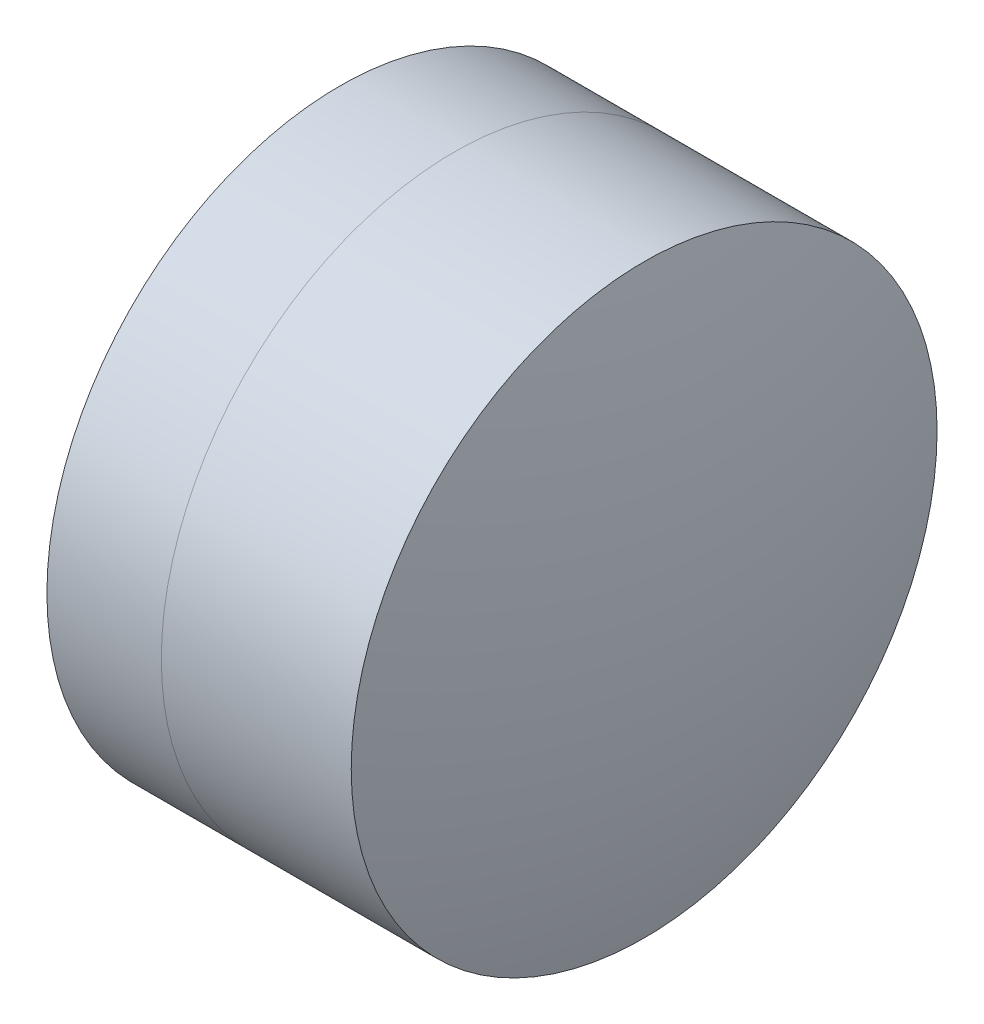
SolidWorks part; units mm, degrees
ref_plane "前视基准面" through (0, 0, 0) normal (0, 0, 1) x (1, 0, 0)
ref_plane "上视基准面" through (0, 0, 0) normal (0, 1, 0) x (1, 0, 0)
ref_plane "右视基准面" through (0, 0, 0) normal (1, 0, 0) x (0, 0, -1)
sketch "草图1" plane through (0, 0, 0) normal (0, 1, 0) x (1, 0, 0)
  line L0 (-0.8161, 0) -> (5.81, 0) construction
  line L1 (1.137, -3.175) -> (2.377, -3.175)
  line L2 (1.137, 3.175) -> (2.377, 3.175)
  arc A0 (2.377, -3.175) -> (2.377, 3.175) centre (-1.342, 0) ccw
  arc A1 (1.137, 3.175) -> (1.137, -3.175) centre (13.898, 0) ccw
  point P4 (5.81, 0)
  point P10 (0.748, 0)
  point P11 (3.548, 0)
  dimension "D3" = 13.15
  dimension "D4" = 4.89
  dimension "D1" = 3.175
  dimension "D2" = 3.175
  dimension "D5" = 2.8
revolve "旋转1" add sketch "草图1" angle 360 about L0
sketch "草图2" plane through (0, 0, 0) normal (0, 1, 0) x (1, 0, 0)
  line L0 (-0.5519, 0) -> (5.6049, 0) construction
  line L2 (2.377, 3.175) -> (4.4353, 3.175)
  line L3 (2.377, -3.175) -> (4.4353, -3.175)
  arc A0 (4.4353, -3.175) -> (4.4353, 3.175) centre (-7.572, 0) ccw
  arc A1 (2.377, -3.175) -> (2.377, 3.175) centre (-1.342, 0) ccw construction
  arc A2 (2.377, -3.175) -> (2.377, 3.175) centre (-1.342, 0) ccw
  point P4 (3.548, 0)
  point P12 (4.848, 0)
  dimension "D1" = 12.42
  dimension "D2" = 1.3
revolve "旋转2" add sketch "草图2" angle 360 about L0
